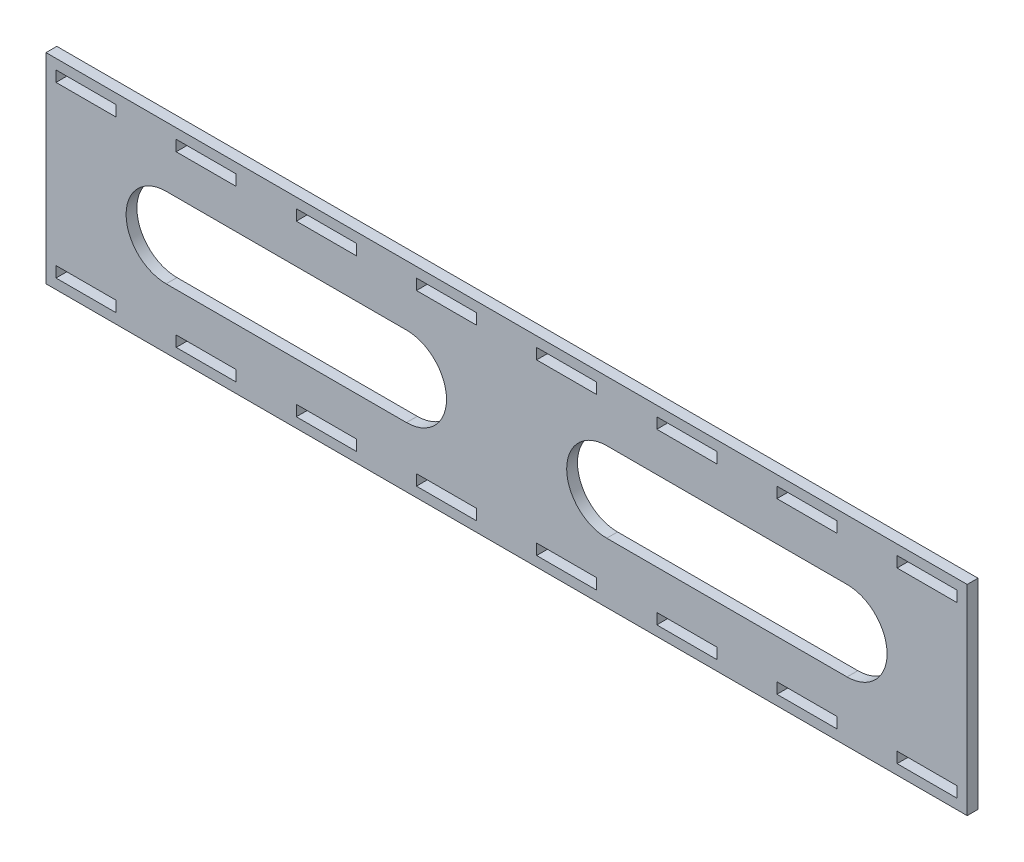
SolidWorks part; units mm, degrees
ref_plane "Front Plane" through (0, 0, 0) normal (0, 0, 1) x (1, 0, 0)
ref_plane "Top Plane" through (0, 0, 0) normal (0, 1, 0) x (1, 0, 0)
ref_plane "Right Plane" through (0, 0, 0) normal (1, 0, 0) x (0, 0, -1)
sketch "Sketch1" plane through (0, 0, 0) normal (0, 0, 1) x (1, 0, 0)
  line L0 (-214.4465, 15.1028) -> (245.5535, 15.1028) construction
  line L1 (-214.4465, 65.1028) -> (245.5535, 65.1028)
  line L2 (-214.4465, 65.1028) -> (-214.4465, -34.8972)
  line L3 (-214.4465, -34.8972) -> (245.5535, -34.8972)
  line L4 (245.5535, 65.1028) -> (245.5535, -34.8972)
  line L9 (-149.4465, 60.1028) -> (-149.4465, 54.7028)
  line L10 (-209.4465, 60.1028) -> (-179.4465, 60.1028)
  line L11 (-209.4465, 60.1028) -> (-209.4465, 54.7028)
  line L12 (-209.4465, 54.7028) -> (-179.4465, 54.7028)
  line L13 (-179.4465, 60.1028) -> (-179.4465, 54.7028)
  line L14 (-149.4465, 60.1028) -> (-119.4465, 60.1028)
  line L15 (-119.4465, 60.1028) -> (-119.4465, 54.7028)
  line L16 (-149.4465, 54.7028) -> (-119.4465, 54.7028)
  line L17 (-89.4465, 60.1028) -> (-89.4465, 54.7028)
  line L18 (-89.4465, 60.1028) -> (-59.4465, 60.1028)
  line L19 (-59.4465, 60.1028) -> (-59.4465, 54.7028)
  line L20 (-89.4465, 54.7028) -> (-59.4465, 54.7028)
  line L21 (-29.4465, 60.1028) -> (-29.4465, 54.7028)
  line L22 (-29.4465, 60.1028) -> (0.5535, 60.1028)
  line L23 (0.5535, 60.1028) -> (0.5535, 54.7028)
  line L24 (-29.4465, 54.7028) -> (0.5535, 54.7028)
  line L25 (30.5535, 60.1028) -> (30.5535, 54.7028)
  line L26 (30.5535, 60.1028) -> (60.5535, 60.1028)
  line L27 (60.5535, 60.1028) -> (60.5535, 54.7028)
  line L28 (30.5535, 54.7028) -> (60.5535, 54.7028)
  line L29 (90.5535, 60.1028) -> (90.5535, 54.7028)
  line L30 (90.5535, 60.1028) -> (120.5535, 60.1028)
  line L31 (120.5535, 60.1028) -> (120.5535, 54.7028)
  line L32 (90.5535, 54.7028) -> (120.5535, 54.7028)
  line L33 (150.5535, 60.1028) -> (150.5535, 54.7028)
  line L34 (150.5535, 60.1028) -> (180.5535, 60.1028)
  line L35 (180.5535, 60.1028) -> (180.5535, 54.7028)
  line L36 (150.5535, 54.7028) -> (180.5535, 54.7028)
  line L37 (210.5535, 60.1028) -> (210.5535, 54.7028)
  line L38 (210.5535, 60.1028) -> (240.5535, 60.1028)
  line L39 (240.5535, 60.1028) -> (240.5535, 54.7028)
  line L40 (210.5535, 54.7028) -> (240.5535, 54.7028)
  line L41 (210.5535, -24.4972) -> (240.5535, -24.4972)
  line L42 (240.5535, -29.8972) -> (240.5535, -24.4972)
  line L43 (210.5535, -29.8972) -> (240.5535, -29.8972)
  line L44 (210.5535, -29.8972) -> (210.5535, -24.4972)
  line L45 (150.5535, -24.4972) -> (180.5535, -24.4972)
  line L46 (180.5535, -29.8972) -> (180.5535, -24.4972)
  line L47 (150.5535, -29.8972) -> (180.5535, -29.8972)
  line L48 (150.5535, -29.8972) -> (150.5535, -24.4972)
  line L49 (90.5535, -24.4972) -> (120.5535, -24.4972)
  line L50 (120.5535, -29.8972) -> (120.5535, -24.4972)
  line L51 (90.5535, -29.8972) -> (120.5535, -29.8972)
  line L52 (90.5535, -29.8972) -> (90.5535, -24.4972)
  line L53 (30.5535, -24.4972) -> (60.5535, -24.4972)
  line L54 (60.5535, -29.8972) -> (60.5535, -24.4972)
  line L55 (30.5535, -29.8972) -> (60.5535, -29.8972)
  line L56 (30.5535, -29.8972) -> (30.5535, -24.4972)
  line L57 (-29.4465, -24.4972) -> (0.5535, -24.4972)
  line L58 (0.5535, -29.8972) -> (0.5535, -24.4972)
  line L59 (-29.4465, -29.8972) -> (0.5535, -29.8972)
  line L60 (-29.4465, -29.8972) -> (-29.4465, -24.4972)
  line L61 (-89.4465, -24.4972) -> (-59.4465, -24.4972)
  line L62 (-59.4465, -29.8972) -> (-59.4465, -24.4972)
  line L63 (-89.4465, -29.8972) -> (-59.4465, -29.8972)
  line L64 (-89.4465, -29.8972) -> (-89.4465, -24.4972)
  line L65 (-149.4465, -24.4972) -> (-119.4465, -24.4972)
  line L66 (-119.4465, -29.8972) -> (-119.4465, -24.4972)
  line L67 (-149.4465, -29.8972) -> (-119.4465, -29.8972)
  line L68 (-179.4465, -29.8972) -> (-179.4465, -24.4972)
  line L69 (-209.4465, -24.4972) -> (-179.4465, -24.4972)
  line L70 (-209.4465, -29.8972) -> (-209.4465, -24.4972)
  line L71 (-209.4465, -29.8972) -> (-179.4465, -29.8972)
  line L72 (-149.4465, -29.8972) -> (-149.4465, -24.4972)
  dimension "D1" = 460
  dimension "D2" = 100
  dimension "D3" = 30
  dimension "D4" = 5.4
  dimension "D5" = 5
  dimension "D6" = 5
  dimension "D7" = 8
extrude "Boss-Extrude1" add sketch "Sketch1" along normal blind 5.4
sketch "Sketch2" plane through (0, 0, 5.4) normal (0, 0, 1) x (1, 0, 0)
  line L0 (-154.4465, 15.1028) -> (-34.4465, 15.1028) construction
  line L1 (-154.4465, 35.1028) -> (-34.4465, 35.1028)
  line L2 (-154.4465, -4.8972) -> (-34.4465, -4.8972)
  line L3 (-214.4465, 65.1028) -> (-214.4465, -34.8972) construction
  line L4 (245.5535, 65.1028) -> (-214.4465, 65.1028) construction
  line L5 (65.5535, -4.8972) -> (185.5535, -4.8972)
  line L6 (65.5535, 35.1028) -> (185.5535, 35.1028)
  line L7 (65.5535, 15.1028) -> (185.5535, 15.1028) construction
  line L9 (245.5535, -34.8972) -> (245.5535, 65.1028) construction
  arc A0 (-154.4465, 35.1028) -> (-154.4465, -4.8972) centre (-154.4465, 15.1028) ccw
  arc A1 (-34.4465, -4.8972) -> (-34.4465, 35.1028) centre (-34.4465, 15.1028) ccw
  arc A2 (65.5535, 35.1028) -> (65.5535, -4.8972) centre (65.5535, 15.1028) ccw
  arc A3 (185.5535, -4.8972) -> (185.5535, 35.1028) centre (185.5535, 15.1028) ccw
  point P2 (-94.4465, 15.1028)
  point P15 (125.5535, 15.1028)
  dimension "D4" = 20
  dimension "D6" = 60
  dimension "D1" = 60
  dimension "D2" = 50
  dimension "D3" = 120
  dimension "D5" = 2
extrude "Cut-Extrude1" cut sketch "Sketch2" against normal through all
